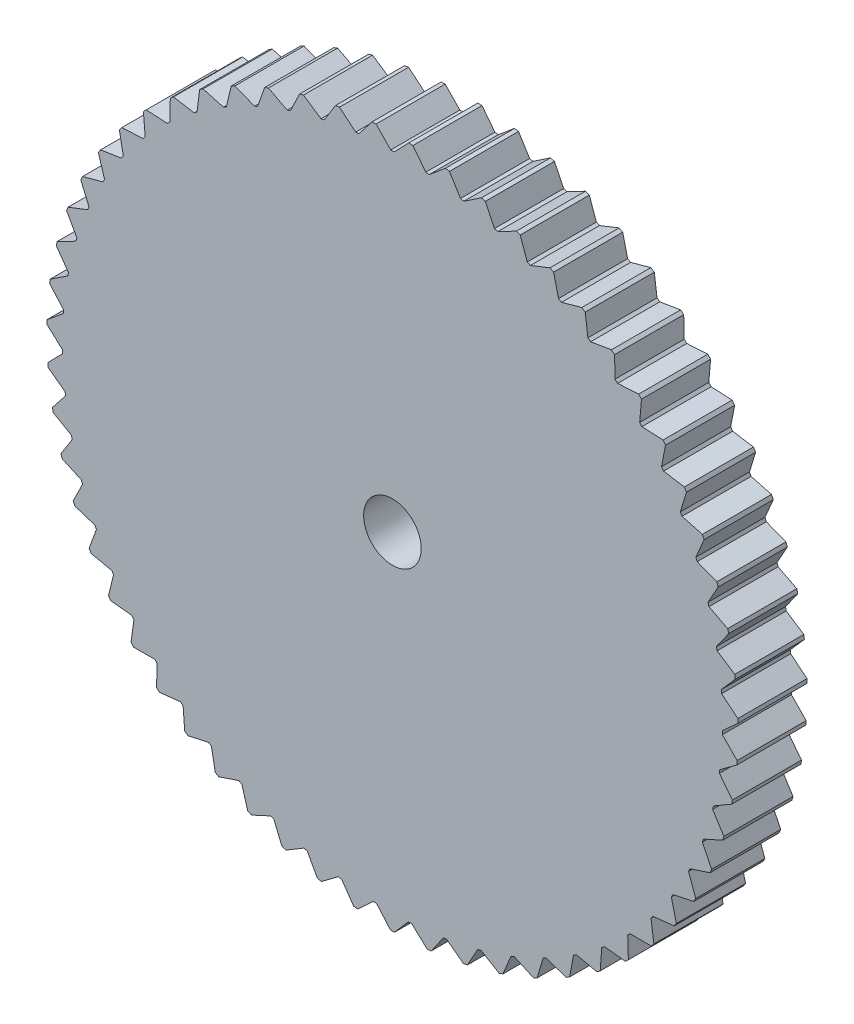
SolidWorks part; units mm, degrees
ref_plane "Front Plane" through (0, 0, 0) normal (0, 0, 1) x (1, 0, 0)
ref_plane "Top Plane" through (0, 0, 0) normal (0, 1, 0) x (1, 0, 0)
ref_plane "Right Plane" through (0, 0, 0) normal (1, 0, 0) x (0, 0, -1)
sketch "Sketch1" plane through (0, 0, 0) normal (0, 0, 1) x (1, 0, 0)
  line L0 (0, 0) -> (0, 60) construction
  line L1 (-3, 61) -> (-0.3, 57.3) construction
  line L2 (0.3, 57.3) -> (3, 61) construction
  line L3 (-0.3, 57.3) -> (0.3, 57.3) construction
  line L4 (-3, 61) -> (3, 61) construction
  line L5 (7.7766, 56.7706) -> (10.9364, 60.0866) construction
  line L6 (4.9878, 60.8697) -> (7.1817, 56.8489) construction
  line L7 (4.9878, 60.8697) -> (10.9364, 60.0866) construction
  line L8 (7.1817, 56.8489) -> (7.7766, 56.7706) construction
  line L9 (15.1201, 55.2699) -> (18.6857, 58.145) construction
  line L10 (12.8902, 59.6979) -> (14.5406, 55.4252) construction
  line L11 (12.8902, 59.6979) -> (18.6857, 58.145) construction
  line L12 (14.5406, 55.4252) -> (15.1201, 55.2699) construction
  line L13 (22.2049, 52.8235) -> (26.1153, 55.2086) construction
  line L14 (20.5721, 57.5047) -> (21.6506, 53.0531) construction
  line L15 (20.5721, 57.5047) -> (26.1153, 55.2086) construction
  line L16 (21.6506, 53.0531) -> (22.2049, 52.8235) construction
  line L17 (28.9098, 49.4733) -> (33.0981, 51.3275) construction
  line L18 (27.9019, 54.3275) -> (28.3902, 49.7733) construction
  line L19 (27.9019, 54.3275) -> (33.0981, 51.3275) construction
  line L20 (28.3902, 49.7733) -> (28.9098, 49.4733) construction
  line L21 (35.12, 45.2765) -> (39.5145, 46.5683) construction
  line L22 (34.7544, 50.2208) -> (34.644, 45.6418) construction
  line L23 (34.7544, 50.2208) -> (39.5145, 46.5683) construction
  line L24 (34.644, 45.6418) -> (35.12, 45.2765) construction
  line L25 (40.7294, 40.3051) -> (45.2548, 41.0122) construction
  line L26 (41.0122, 45.2548) -> (40.3051, 40.7294) construction
  line L27 (41.0122, 45.2548) -> (45.2548, 41.0122) construction
  line L28 (40.3051, 40.7294) -> (40.7294, 40.3051) construction
  line L29 (45.6418, 34.644) -> (50.2208, 34.7544) construction
  line L30 (46.5683, 39.5145) -> (45.2765, 35.12) construction
  line L31 (46.5683, 39.5145) -> (50.2208, 34.7544) construction
  line L32 (45.2765, 35.12) -> (45.6418, 34.644) construction
  line L33 (49.7733, 28.3902) -> (54.3275, 27.9019) construction
  line L34 (51.3275, 33.0981) -> (49.4733, 28.9098) construction
  line L35 (51.3275, 33.0981) -> (54.3275, 27.9019) construction
  line L36 (49.4733, 28.9098) -> (49.7733, 28.3902) construction
  line L37 (53.0531, 21.6506) -> (57.5047, 20.5721) construction
  line L38 (55.2086, 26.1153) -> (52.8235, 22.2049) construction
  line L39 (55.2086, 26.1153) -> (57.5047, 20.5721) construction
  line L40 (52.8235, 22.2049) -> (53.0531, 21.6506) construction
  line L41 (55.4252, 14.5406) -> (59.6979, 12.8902) construction
  line L42 (58.145, 18.6857) -> (55.2699, 15.1201) construction
  line L43 (58.145, 18.6857) -> (59.6979, 12.8902) construction
  line L44 (55.2699, 15.1201) -> (55.4252, 14.5406) construction
  line L45 (56.8489, 7.1817) -> (60.8697, 4.9878) construction
  line L46 (60.0866, 10.9364) -> (56.7706, 7.7766) construction
  line L47 (60.0866, 10.9364) -> (60.8697, 4.9878) construction
  line L48 (56.7706, 7.7766) -> (56.8489, 7.1817) construction
  line L49 (57.3, -0.3) -> (61, -3) construction
  line L50 (61, 3) -> (57.3, 0.3) construction
  line L51 (61, 3) -> (61, -3) construction
  line L52 (57.3, 0.3) -> (57.3, -0.3) construction
  line L53 (56.7706, -7.7766) -> (60.0866, -10.9364) construction
  line L54 (60.8697, -4.9878) -> (56.8489, -7.1817) construction
  line L55 (60.8697, -4.9878) -> (60.0866, -10.9364) construction
  line L56 (56.8489, -7.1817) -> (56.7706, -7.7766) construction
  line L57 (55.2699, -15.1201) -> (58.145, -18.6857) construction
  line L58 (59.6979, -12.8902) -> (55.4252, -14.5406) construction
  line L59 (59.6979, -12.8902) -> (58.145, -18.6857) construction
  line L60 (55.4252, -14.5406) -> (55.2699, -15.1201) construction
  line L61 (52.8235, -22.2049) -> (55.2086, -26.1153) construction
  line L62 (57.5047, -20.5721) -> (53.0531, -21.6506) construction
  line L63 (57.5047, -20.5721) -> (55.2086, -26.1153) construction
  line L64 (53.0531, -21.6506) -> (52.8235, -22.2049) construction
  line L65 (49.4733, -28.9098) -> (51.3275, -33.0981) construction
  line L66 (54.3275, -27.9019) -> (49.7733, -28.3902) construction
  line L67 (54.3275, -27.9019) -> (51.3275, -33.0981) construction
  line L68 (49.7733, -28.3902) -> (49.4733, -28.9098) construction
  line L69 (45.2765, -35.12) -> (46.5683, -39.5145) construction
  line L70 (50.2208, -34.7544) -> (45.6418, -34.644) construction
  line L71 (50.2208, -34.7544) -> (46.5683, -39.5145) construction
  line L72 (45.6418, -34.644) -> (45.2765, -35.12) construction
  line L73 (40.3051, -40.7294) -> (41.0122, -45.2548) construction
  line L74 (45.2548, -41.0122) -> (40.7294, -40.3051) construction
  line L75 (45.2548, -41.0122) -> (41.0122, -45.2548) construction
  line L76 (40.7294, -40.3051) -> (40.3051, -40.7294) construction
  line L77 (34.644, -45.6418) -> (34.7544, -50.2208) construction
  line L78 (39.5145, -46.5683) -> (35.12, -45.2765) construction
  line L79 (39.5145, -46.5683) -> (34.7544, -50.2208) construction
  line L80 (35.12, -45.2765) -> (34.644, -45.6418) construction
  line L81 (28.3902, -49.7733) -> (27.9019, -54.3275) construction
  line L82 (33.0981, -51.3275) -> (28.9098, -49.4733) construction
  line L83 (33.0981, -51.3275) -> (27.9019, -54.3275) construction
  line L84 (28.9098, -49.4733) -> (28.3902, -49.7733) construction
  line L85 (21.6506, -53.0531) -> (20.5721, -57.5047) construction
  line L86 (26.1153, -55.2086) -> (22.2049, -52.8235) construction
  line L87 (26.1153, -55.2086) -> (20.5721, -57.5047) construction
  line L88 (22.2049, -52.8235) -> (21.6506, -53.0531) construction
  line L89 (14.5406, -55.4252) -> (12.8902, -59.6979) construction
  line L90 (18.6857, -58.145) -> (15.1201, -55.2699) construction
  line L91 (18.6857, -58.145) -> (12.8902, -59.6979) construction
  line L92 (15.1201, -55.2699) -> (14.5406, -55.4252) construction
  line L93 (7.1817, -56.8489) -> (4.9878, -60.8697) construction
  line L94 (10.9364, -60.0866) -> (7.7766, -56.7706) construction
  line L95 (10.9364, -60.0866) -> (4.9878, -60.8697) construction
  line L96 (7.7766, -56.7706) -> (7.1817, -56.8489) construction
  line L97 (-0.3, -57.3) -> (-3, -61) construction
  line L98 (3, -61) -> (0.3, -57.3) construction
  line L99 (3, -61) -> (-3, -61) construction
  line L100 (0.3, -57.3) -> (-0.3, -57.3) construction
  line L101 (-7.7766, -56.7706) -> (-10.9364, -60.0866) construction
  line L102 (-4.9878, -60.8697) -> (-7.1817, -56.8489) construction
  line L103 (-4.9878, -60.8697) -> (-10.9364, -60.0866) construction
  line L104 (-7.1817, -56.8489) -> (-7.7766, -56.7706) construction
  line L105 (-15.1201, -55.2699) -> (-18.6857, -58.145) construction
  line L106 (-12.8902, -59.6979) -> (-14.5406, -55.4252) construction
  line L107 (-12.8902, -59.6979) -> (-18.6857, -58.145) construction
  line L108 (-14.5406, -55.4252) -> (-15.1201, -55.2699) construction
  line L109 (-22.2049, -52.8235) -> (-26.1153, -55.2086) construction
  line L110 (-20.5721, -57.5047) -> (-21.6506, -53.0531) construction
  line L111 (-20.5721, -57.5047) -> (-26.1153, -55.2086) construction
  line L112 (-21.6506, -53.0531) -> (-22.2049, -52.8235) construction
  line L113 (-28.9098, -49.4733) -> (-33.0981, -51.3275) construction
  line L114 (-27.9019, -54.3275) -> (-28.3902, -49.7733) construction
  line L115 (-27.9019, -54.3275) -> (-33.0981, -51.3275) construction
  line L116 (-28.3902, -49.7733) -> (-28.9098, -49.4733) construction
  line L117 (-35.12, -45.2765) -> (-39.5145, -46.5683) construction
  line L118 (-34.7544, -50.2208) -> (-34.644, -45.6418) construction
  line L119 (-34.7544, -50.2208) -> (-39.5145, -46.5683) construction
  line L120 (-34.644, -45.6418) -> (-35.12, -45.2765) construction
  line L121 (-40.7294, -40.3051) -> (-45.2548, -41.0122) construction
  line L122 (-41.0122, -45.2548) -> (-40.3051, -40.7294) construction
  line L123 (-41.0122, -45.2548) -> (-45.2548, -41.0122) construction
  line L124 (-40.3051, -40.7294) -> (-40.7294, -40.3051) construction
  line L125 (-45.6418, -34.644) -> (-50.2208, -34.7544) construction
  line L126 (-46.5683, -39.5145) -> (-45.2765, -35.12) construction
  line L127 (-46.5683, -39.5145) -> (-50.2208, -34.7544) construction
  line L128 (-45.2765, -35.12) -> (-45.6418, -34.644) construction
  line L129 (-49.7733, -28.3902) -> (-54.3275, -27.9019) construction
  line L130 (-51.3275, -33.0981) -> (-49.4733, -28.9098) construction
  line L131 (-51.3275, -33.0981) -> (-54.3275, -27.9019) construction
  line L132 (-49.4733, -28.9098) -> (-49.7733, -28.3902) construction
  line L133 (-53.0531, -21.6506) -> (-57.5047, -20.5721) construction
  line L134 (-55.2086, -26.1153) -> (-52.8235, -22.2049) construction
  line L135 (-55.2086, -26.1153) -> (-57.5047, -20.5721) construction
  line L136 (-52.8235, -22.2049) -> (-53.0531, -21.6506) construction
  line L137 (-55.4252, -14.5406) -> (-59.6979, -12.8902) construction
  line L138 (-58.145, -18.6857) -> (-55.2699, -15.1201) construction
  line L139 (-58.145, -18.6857) -> (-59.6979, -12.8902) construction
  line L140 (-55.2699, -15.1201) -> (-55.4252, -14.5406) construction
  line L141 (-56.8489, -7.1817) -> (-60.8697, -4.9878) construction
  line L142 (-60.0866, -10.9364) -> (-56.7706, -7.7766) construction
  line L143 (-60.0866, -10.9364) -> (-60.8697, -4.9878) construction
  line L144 (-56.7706, -7.7766) -> (-56.8489, -7.1817) construction
  line L145 (-57.3, 0.3) -> (-61, 3) construction
  line L146 (-61, -3) -> (-57.3, -0.3) construction
  line L147 (-61, -3) -> (-61, 3) construction
  line L148 (-57.3, -0.3) -> (-57.3, 0.3) construction
  line L149 (-56.7706, 7.7766) -> (-60.0866, 10.9364) construction
  line L150 (-60.8697, 4.9878) -> (-56.8489, 7.1817) construction
  line L151 (-60.8697, 4.9878) -> (-60.0866, 10.9364) construction
  line L152 (-56.8489, 7.1817) -> (-56.7706, 7.7766) construction
  line L153 (-55.2699, 15.1201) -> (-58.145, 18.6857) construction
  line L154 (-59.6979, 12.8902) -> (-55.4252, 14.5406) construction
  line L155 (-59.6979, 12.8902) -> (-58.145, 18.6857) construction
  line L156 (-55.4252, 14.5406) -> (-55.2699, 15.1201) construction
  line L157 (-52.8235, 22.2049) -> (-55.2086, 26.1153) construction
  line L158 (-57.5047, 20.5721) -> (-53.0531, 21.6506) construction
  line L159 (-57.5047, 20.5721) -> (-55.2086, 26.1153) construction
  line L160 (-53.0531, 21.6506) -> (-52.8235, 22.2049) construction
  line L161 (-49.4733, 28.9098) -> (-51.3275, 33.0981) construction
  line L162 (-54.3275, 27.9019) -> (-49.7733, 28.3902) construction
  line L163 (-54.3275, 27.9019) -> (-51.3275, 33.0981) construction
  line L164 (-49.7733, 28.3902) -> (-49.4733, 28.9098) construction
  line L165 (-45.2765, 35.12) -> (-46.5683, 39.5145) construction
  line L166 (-50.2208, 34.7544) -> (-45.6418, 34.644) construction
  line L167 (-50.2208, 34.7544) -> (-46.5683, 39.5145) construction
  line L168 (-45.6418, 34.644) -> (-45.2765, 35.12) construction
  line L169 (-40.3051, 40.7294) -> (-41.0122, 45.2548) construction
  line L170 (-45.2548, 41.0122) -> (-40.7294, 40.3051) construction
  line L171 (-45.2548, 41.0122) -> (-41.0122, 45.2548) construction
  line L172 (-40.7294, 40.3051) -> (-40.3051, 40.7294) construction
  line L173 (-34.644, 45.6418) -> (-34.7544, 50.2208) construction
  line L174 (-39.5145, 46.5683) -> (-35.12, 45.2765) construction
  line L175 (-39.5145, 46.5683) -> (-34.7544, 50.2208) construction
  line L176 (-35.12, 45.2765) -> (-34.644, 45.6418) construction
  line L177 (-28.3902, 49.7733) -> (-27.9019, 54.3275) construction
  line L178 (-33.0981, 51.3275) -> (-28.9098, 49.4733) construction
  line L179 (-33.0981, 51.3275) -> (-27.9019, 54.3275) construction
  line L180 (-28.9098, 49.4733) -> (-28.3902, 49.7733) construction
  line L181 (-21.6506, 53.0531) -> (-20.5721, 57.5047) construction
  line L182 (-26.1153, 55.2086) -> (-22.2049, 52.8235) construction
  line L183 (-26.1153, 55.2086) -> (-20.5721, 57.5047) construction
  line L184 (-22.2049, 52.8235) -> (-21.6506, 53.0531) construction
  line L185 (-14.5406, 55.4252) -> (-12.8902, 59.6979) construction
  line L186 (-18.6857, 58.145) -> (-15.1201, 55.2699) construction
  line L187 (-18.6857, 58.145) -> (-12.8902, 59.6979) construction
  line L188 (-15.1201, 55.2699) -> (-14.5406, 55.4252) construction
  line L189 (-7.1817, 56.8489) -> (-4.9878, 60.8697) construction
  line L190 (-10.9364, 60.0866) -> (-7.7766, 56.7706) construction
  line L191 (-10.9364, 60.0866) -> (-4.9878, 60.8697) construction
  line L192 (-7.7766, 56.7706) -> (-7.1817, 56.8489) construction
  circle A0 centre (0, 0) radius 60
  circle A1 centre (0, 0) radius 5
  point P200 (0, 0)
  dimension "D1" = 10
  dimension "D2" = 120
  dimension "D3" = 0.6
  dimension "D4" = 6
  dimension "D5" = 3.7
  dimension "D6" = 1
  dimension "D7" = 48
extrude "Boss-Extrude1" add sketch "Sketch1" along normal blind 12 contours A1 | A0
sketch "Sketch2" plane through (0, 0, 12) normal (0, 0, 1) x (1, 0, 0)
  line L0 (0, 0) -> (0, 60) construction
  line L1 (-3, 60.1) -> (-0.3, 57.3)
  line L2 (0.3, 57.3) -> (3, 60.1)
  line L3 (-0.3, 57.3) -> (0.3, 57.3)
  line L4 (-3, 60.1) -> (3, 60.1)
  line L5 (3.4052, 60.0784) -> (5.7923, 57.0073)
  line L6 (6.3889, 56.9435) -> (9.3712, 59.4406)
  line L7 (5.7923, 57.0073) -> (6.3889, 56.9435)
  line L8 (3.4052, 60.0784) -> (9.3712, 59.4406)
  line L9 (0, 0) -> (6.3776, 59.6601) construction
  line L10 (9.7719, 59.3761) -> (11.819, 56.0686)
  line L11 (12.4054, 55.9418) -> (15.6363, 58.1078)
  line L12 (11.819, 56.0686) -> (12.4054, 55.9418)
  line L13 (9.7719, 59.3761) -> (15.6363, 58.1078)
  line L14 (0, 0) -> (12.683, 58.6442) construction
  line L15 (16.0278, 58.001) -> (17.7118, 54.4947)
  line L16 (18.2814, 54.3063) -> (21.7242, 56.1166)
  line L17 (17.7118, 54.4947) -> (18.2814, 54.3063)
  line L18 (16.0278, 58.001) -> (21.7242, 56.1166)
  line L19 (0, 0) -> (18.8446, 56.9639) construction
  line L20 (22.1021, 55.9688) -> (23.4039, 52.3033)
  line L21 (23.9502, 52.0554) -> (27.566, 53.4895)
  line L22 (23.4039, 52.3033) -> (23.9502, 52.0554)
  line L23 (22.1021, 55.9688) -> (27.566, 53.4895)
  line L24 (0, 0) -> (24.7927, 54.6381) construction
  line L25 (27.9261, 53.3024) -> (28.8308, 49.5193)
  line L26 (29.3477, 49.2147) -> (33.0954, 50.2564)
  line L27 (28.8308, 49.5193) -> (29.3477, 49.2147)
  line L28 (27.9261, 53.3024) -> (33.0954, 50.2564)
  line L29 (0, 0) -> (30.4599, 51.6932) construction
  line L30 (33.4335, 50.0321) -> (33.931, 46.1743)
  line L31 (34.4127, 45.8165) -> (38.2498, 46.4539)
  line L32 (33.931, 46.1743) -> (34.4127, 45.8165)
  line L33 (33.4335, 50.0321) -> (38.2498, 46.4539)
  line L34 (0, 0) -> (35.782, 48.1627) construction
  line L35 (38.5622, 46.1949) -> (38.6468, 42.3061)
  line L36 (39.0877, 41.8991) -> (42.9709, 42.125)
  line L37 (38.6468, 42.3061) -> (39.0877, 41.8991)
  line L38 (38.5622, 46.1949) -> (42.9709, 42.125)
  line L39 (0, 0) -> (40.6987, 44.0864) construction
  line L40 (43.254, 41.8342) -> (42.9248, 37.9585)
  line L41 (43.3199, 37.5069) -> (47.205, 37.3188)
  line L42 (42.9248, 37.9585) -> (43.3199, 37.5069)
  line L43 (43.254, 41.8342) -> (47.205, 37.3188)
  line L44 (0, 0) -> (45.1542, 39.5107) construction
  line L45 (47.4556, 36.9996) -> (46.7163, 33.1808)
  line L46 (47.0612, 32.6898) -> (50.9044, 32.0898)
  line L47 (46.7163, 33.1808) -> (47.0612, 32.6898)
  line L48 (47.4556, 36.9996) -> (50.9044, 32.0898)
  line L49 (0, 0) -> (49.0982, 34.4872) construction
  line L50 (51.1196, 31.7458) -> (49.9786, 28.0272)
  line L51 (50.2693, 27.5023) -> (54.0269, 26.4972)
  line L52 (49.9786, 28.0272) -> (50.2693, 27.5023)
  line L53 (51.1196, 31.7458) -> (54.0269, 26.4972)
  line L54 (0, 0) -> (52.4858, 29.0731) construction
  line L55 (54.2044, 26.1323) -> (52.6745, 22.556)
  line L56 (52.9078, 22.0032) -> (56.5373, 20.6044)
  line L57 (52.6745, 22.556) -> (52.9078, 22.0032)
  line L58 (54.2044, 26.1323) -> (56.5373, 20.6044)
  line L59 (0, 0) -> (55.2787, 23.3295) construction
  line L60 (56.675, 20.2227) -> (54.7737, 16.8293)
  line L61 (54.9469, 16.2548) -> (58.4071, 14.4781)
  line L62 (54.7737, 16.8293) -> (54.9469, 16.2548)
  line L63 (56.675, 20.2227) -> (58.4071, 14.4781)
  line L64 (0, 0) -> (57.4453, 17.3215) construction
  line L65 (58.5034, 14.0839) -> (56.2522, 10.9118)
  line L66 (56.3634, 10.3222) -> (59.6152, 8.1878)
  line L67 (56.2522, 10.9118) -> (56.3634, 10.3222)
  line L68 (58.5034, 14.0839) -> (59.6152, 8.1878)
  line L69 (0, 0) -> (58.961, 11.1173) construction
  line L70 (59.669, 7.7856) -> (57.0934, 4.8708)
  line L71 (57.1413, 4.2727) -> (60.1478, 1.8047)
  line L72 (57.0934, 4.8708) -> (57.1413, 4.2727)
  line L73 (59.669, 7.7856) -> (60.1478, 1.8047)
  line L74 (0, 0) -> (59.8087, 4.7872) construction
  line L75 (60.1586, 1.399) -> (57.2877, -1.2255)
  line L76 (57.2717, -1.8252) -> (59.9988, -4.5988)
  line L77 (57.2877, -1.2255) -> (57.2717, -1.8252)
  line L78 (60.1586, 1.399) -> (59.9988, -4.5988)
  line L79 (0, 0) -> (59.9787, -1.5972) construction
  line L80 (59.9665, -5.0033) -> (56.8329, -7.3078)
  line L81 (56.7532, -7.9025) -> (59.1701, -10.9503)
  line L82 (56.8329, -7.3078) -> (56.7532, -7.9025)
  line L83 (59.9665, -5.0033) -> (59.1701, -10.9503)
  line L84 (0, 0) -> (59.4692, -7.9635) construction
  line L85 (59.0949, -11.349) -> (55.7341, -13.3074)
  line L86 (55.5917, -13.8902) -> (57.671, -17.1776)
  line L87 (55.7341, -13.3074) -> (55.5917, -13.8902)
  line L88 (59.0949, -11.349) -> (57.671, -17.1776)
  line L89 (0, 0) -> (58.2858, -14.2396) construction
  line L90 (57.5538, -17.5662) -> (54.0039, -19.1562)
  line L91 (53.8004, -19.7206) -> (55.5184, -23.2104)
  line L92 (54.0039, -19.1562) -> (53.8004, -19.7206)
  line L93 (57.5538, -17.5662) -> (55.5184, -23.2104)
  line L94 (0, 0) -> (56.442, -20.3543) construction
  line L95 (55.3606, -23.5842) -> (51.6618, -24.7879)
  line L96 (51.3994, -25.3275) -> (52.7367, -28.9801)
  line L97 (51.6618, -24.7879) -> (51.3994, -25.3275)
  line L98 (55.3606, -23.5842) -> (52.7367, -28.9801)
  line L99 (0, 0) -> (53.9587, -26.2384) construction
  line L100 (52.5401, -29.3351) -> (48.7343, -30.1388)
  line L101 (48.4161, -30.6474) -> (49.3576, -34.4215)
  line L102 (48.7343, -30.1388) -> (48.4161, -30.6474)
  line L103 (52.5401, -29.3351) -> (49.3576, -34.4215)
  line L104 (0, 0) -> (50.8641, -31.8253) construction
  line L105 (49.1243, -34.7536) -> (45.2547, -35.1482)
  line L106 (44.8841, -35.6201) -> (45.4192, -39.4729)
  line L107 (45.2547, -35.1482) -> (44.8841, -35.6201)
  line L108 (49.1243, -34.7536) -> (45.4192, -39.4729)
  line L109 (0, 0) -> (47.1931, -37.0515) construction
  line L110 (45.1519, -39.7783) -> (41.2623, -39.7593)
  line L111 (40.8437, -40.1892) -> (40.9662, -44.077)
  line L112 (41.2623, -39.7593) -> (40.8437, -40.1892)
  line L113 (45.1519, -39.7783) -> (40.9662, -44.077)
  line L114 (0, 0) -> (42.9874, -41.8579) construction
  line L115 (40.668, -44.3523) -> (36.8023, -43.92)
  line L116 (36.3404, -44.303) -> (36.049, -48.1818)
  line L117 (36.8023, -43.92) -> (36.3404, -44.303)
  line L118 (40.668, -44.3523) -> (36.049, -48.1818)
  line L119 (0, 0) -> (38.2947, -46.19) construction
  line L120 (35.7232, -48.4238) -> (31.9254, -47.583)
  line L121 (31.4254, -47.9147) -> (30.7233, -51.7406)
  line L122 (31.9254, -47.583) -> (31.4254, -47.9147)
  line L123 (35.7232, -48.4238) -> (30.7233, -51.7406)
  line L124 (0, 0) -> (33.168, -49.9988) construction
  line L125 (30.3737, -51.9466) -> (26.6868, -50.7069)
  line L126 (26.1544, -50.9836) -> (25.0496, -54.7131)
  line L127 (26.6868, -50.7069) -> (26.1544, -50.9836)
  line L128 (30.3737, -51.9466) -> (25.0496, -54.7131)
  line L129 (0, 0) -> (27.6656, -53.2411) construction
  line L130 (24.6801, -54.8808) -> (21.1458, -53.2563)
  line L131 (20.587, -53.4748) -> (19.092, -57.0658)
  line L132 (21.1458, -53.2563) -> (20.587, -53.4748)
  line L133 (24.6801, -54.8808) -> (19.092, -57.0658)
  line L134 (0, 0) -> (21.8496, -55.8802) construction
  line L135 (18.7068, -57.1932) -> (15.3652, -55.2023)
  line L136 (14.7863, -55.3601) -> (12.9182, -58.7719)
  line L137 (15.3652, -55.2023) -> (14.7863, -55.3601)
  line L138 (18.7068, -57.1932) -> (12.9182, -58.7719)
  line L139 (0, 0) -> (15.7862, -57.8861) construction
  line L140 (12.5215, -58.8576) -> (9.4105, -56.5228)
  line L141 (8.8182, -56.6182) -> (6.5979, -59.812)
  line L142 (9.4105, -56.5228) -> (8.8182, -56.6182)
  line L143 (12.5215, -58.8576) -> (6.5979, -59.812)
  line L144 (0, 0) -> (9.5438, -59.2361) construction
  line L145 (6.1944, -59.8552) -> (3.3492, -57.2028)
  line L146 (2.7501, -57.2348) -> (0.2029, -60.1745)
  line L147 (3.3492, -57.2028) -> (2.7501, -57.2348)
  line L148 (6.1944, -59.8552) -> (0.2029, -60.1745)
  line L149 (0, 0) -> (3.1933, -59.915) construction
  line L150 (-0.2029, -60.1745) -> (-2.7501, -57.2348)
  line L151 (-3.3492, -57.2028) -> (-6.1944, -59.8552)
  line L152 (-2.7501, -57.2348) -> (-3.3492, -57.2028)
  line L153 (-0.2029, -60.1745) -> (-6.1944, -59.8552)
  line L154 (0, 0) -> (-3.1933, -59.915) construction
  line L155 (-6.5979, -59.812) -> (-8.8182, -56.6182)
  line L156 (-9.4105, -56.5228) -> (-12.5215, -58.8576)
  line L157 (-8.8182, -56.6182) -> (-9.4105, -56.5228)
  line L158 (-6.5979, -59.812) -> (-12.5215, -58.8576)
  line L159 (0, 0) -> (-9.5438, -59.2361) construction
  line L160 (-12.9182, -58.7719) -> (-14.7863, -55.3601)
  line L161 (-15.3652, -55.2023) -> (-18.7068, -57.1932)
  line L162 (-14.7863, -55.3601) -> (-15.3652, -55.2023)
  line L163 (-12.9182, -58.7719) -> (-18.7068, -57.1932)
  line L164 (0, 0) -> (-15.7862, -57.8861) construction
  line L165 (-19.092, -57.0658) -> (-20.587, -53.4748)
  line L166 (-21.1458, -53.2563) -> (-24.6801, -54.8808)
  line L167 (-20.587, -53.4748) -> (-21.1458, -53.2563)
  line L168 (-19.092, -57.0658) -> (-24.6801, -54.8808)
  line L169 (0, 0) -> (-21.8496, -55.8802) construction
  line L170 (-25.0496, -54.7131) -> (-26.1544, -50.9836)
  line L171 (-26.6868, -50.7069) -> (-30.3737, -51.9466)
  line L172 (-26.1544, -50.9836) -> (-26.6868, -50.7069)
  line L173 (-25.0496, -54.7131) -> (-30.3737, -51.9466)
  line L174 (0, 0) -> (-27.6656, -53.2411) construction
  line L175 (-30.7233, -51.7406) -> (-31.4254, -47.9147)
  line L176 (-31.9254, -47.583) -> (-35.7232, -48.4238)
  line L177 (-31.4254, -47.9147) -> (-31.9254, -47.583)
  line L178 (-30.7233, -51.7406) -> (-35.7232, -48.4238)
  line L179 (0, 0) -> (-33.168, -49.9988) construction
  line L180 (-36.049, -48.1818) -> (-36.3404, -44.303)
  line L181 (-36.8023, -43.92) -> (-40.668, -44.3523)
  line L182 (-36.3404, -44.303) -> (-36.8023, -43.92)
  line L183 (-36.049, -48.1818) -> (-40.668, -44.3523)
  line L184 (0, 0) -> (-38.2947, -46.19) construction
  line L185 (-40.9662, -44.077) -> (-40.8437, -40.1892)
  line L186 (-41.2623, -39.7593) -> (-45.1519, -39.7783)
  line L187 (-40.8437, -40.1892) -> (-41.2623, -39.7593)
  line L188 (-40.9662, -44.077) -> (-45.1519, -39.7783)
  line L189 (0, 0) -> (-42.9874, -41.8579) construction
  line L190 (-45.4192, -39.4729) -> (-44.8841, -35.6201)
  line L191 (-45.2547, -35.1482) -> (-49.1243, -34.7536)
  line L192 (-44.8841, -35.6201) -> (-45.2547, -35.1482)
  line L193 (-45.4192, -39.4729) -> (-49.1243, -34.7536)
  line L194 (0, 0) -> (-47.1931, -37.0515) construction
  line L195 (-49.3576, -34.4215) -> (-48.4161, -30.6474)
  line L196 (-48.7343, -30.1388) -> (-52.5401, -29.3351)
  line L197 (-48.4161, -30.6474) -> (-48.7343, -30.1388)
  line L198 (-49.3576, -34.4215) -> (-52.5401, -29.3351)
  line L199 (0, 0) -> (-50.8641, -31.8253) construction
  line L200 (-52.7367, -28.9801) -> (-51.3994, -25.3275)
  line L201 (-51.6618, -24.7879) -> (-55.3606, -23.5842)
  line L202 (-51.3994, -25.3275) -> (-51.6618, -24.7879)
  line L203 (-52.7367, -28.9801) -> (-55.3606, -23.5842)
  line L204 (0, 0) -> (-53.9587, -26.2384) construction
  line L205 (-55.5184, -23.2104) -> (-53.8004, -19.7206)
  line L206 (-54.0039, -19.1562) -> (-57.5538, -17.5662)
  line L207 (-53.8004, -19.7206) -> (-54.0039, -19.1562)
  line L208 (-55.5184, -23.2104) -> (-57.5538, -17.5662)
  line L209 (0, 0) -> (-56.442, -20.3543) construction
  line L210 (-57.671, -17.1776) -> (-55.5917, -13.8902)
  line L211 (-55.7341, -13.3074) -> (-59.0949, -11.349)
  line L212 (-55.5917, -13.8902) -> (-55.7341, -13.3074)
  line L213 (-57.671, -17.1776) -> (-59.0949, -11.349)
  line L214 (0, 0) -> (-58.2858, -14.2396) construction
  line L215 (-59.1701, -10.9503) -> (-56.7532, -7.9025)
  line L216 (-56.8329, -7.3078) -> (-59.9665, -5.0033)
  line L217 (-56.7532, -7.9025) -> (-56.8329, -7.3078)
  line L218 (-59.1701, -10.9503) -> (-59.9665, -5.0033)
  line L219 (0, 0) -> (-59.4692, -7.9635) construction
  line L220 (-59.9988, -4.5988) -> (-57.2717, -1.8252)
  line L221 (-57.2877, -1.2255) -> (-60.1586, 1.399)
  line L222 (-57.2717, -1.8252) -> (-57.2877, -1.2255)
  line L223 (-59.9988, -4.5988) -> (-60.1586, 1.399)
  line L224 (0, 0) -> (-59.9787, -1.5972) construction
  line L225 (-60.1478, 1.8047) -> (-57.1413, 4.2727)
  line L226 (-57.0934, 4.8708) -> (-59.669, 7.7856)
  line L227 (-57.1413, 4.2727) -> (-57.0934, 4.8708)
  line L228 (-60.1478, 1.8047) -> (-59.669, 7.7856)
  line L229 (0, 0) -> (-59.8087, 4.7872) construction
  line L230 (-59.6152, 8.1878) -> (-56.3634, 10.3222)
  line L231 (-56.2522, 10.9118) -> (-58.5034, 14.0839)
  line L232 (-56.3634, 10.3222) -> (-56.2522, 10.9118)
  line L233 (-59.6152, 8.1878) -> (-58.5034, 14.0839)
  line L234 (0, 0) -> (-58.961, 11.1173) construction
  line L235 (-58.4071, 14.4781) -> (-54.9469, 16.2548)
  line L236 (-54.7737, 16.8293) -> (-56.675, 20.2227)
  line L237 (-54.9469, 16.2548) -> (-54.7737, 16.8293)
  line L238 (-58.4071, 14.4781) -> (-56.675, 20.2227)
  line L239 (0, 0) -> (-57.4453, 17.3215) construction
  line L240 (-56.5373, 20.6044) -> (-52.9078, 22.0032)
  line L241 (-52.6745, 22.556) -> (-54.2044, 26.1323)
  line L242 (-52.9078, 22.0032) -> (-52.6745, 22.556)
  line L243 (-56.5373, 20.6044) -> (-54.2044, 26.1323)
  line L244 (0, 0) -> (-55.2787, 23.3295) construction
  line L245 (-54.0269, 26.4972) -> (-50.2693, 27.5023)
  line L246 (-49.9786, 28.0272) -> (-51.1196, 31.7458)
  line L247 (-50.2693, 27.5023) -> (-49.9786, 28.0272)
  line L248 (-54.0269, 26.4972) -> (-51.1196, 31.7458)
  line L249 (0, 0) -> (-52.4858, 29.0731) construction
  line L250 (-50.9044, 32.0898) -> (-47.0612, 32.6898)
  line L251 (-46.7163, 33.1808) -> (-47.4556, 36.9996)
  line L252 (-47.0612, 32.6898) -> (-46.7163, 33.1808)
  line L253 (-50.9044, 32.0898) -> (-47.4556, 36.9996)
  line L254 (0, 0) -> (-49.0982, 34.4872) construction
  line L255 (-47.205, 37.3188) -> (-43.3199, 37.5069)
  line L256 (-42.9248, 37.9585) -> (-43.254, 41.8342)
  line L257 (-43.3199, 37.5069) -> (-42.9248, 37.9585)
  line L258 (-47.205, 37.3188) -> (-43.254, 41.8342)
  line L259 (0, 0) -> (-45.1542, 39.5107) construction
  line L260 (-42.9709, 42.125) -> (-39.0877, 41.8991)
  line L261 (-38.6468, 42.3061) -> (-38.5622, 46.1949)
  line L262 (-39.0877, 41.8991) -> (-38.6468, 42.3061)
  line L263 (-42.9709, 42.125) -> (-38.5622, 46.1949)
  line L264 (0, 0) -> (-40.6987, 44.0864) construction
  line L265 (-38.2498, 46.4539) -> (-34.4127, 45.8165)
  line L266 (-33.931, 46.1743) -> (-33.4335, 50.0321)
  line L267 (-34.4127, 45.8165) -> (-33.931, 46.1743)
  line L268 (-38.2498, 46.4539) -> (-33.4335, 50.0321)
  line L269 (0, 0) -> (-35.782, 48.1627) construction
  line L270 (-33.0954, 50.2564) -> (-29.3477, 49.2147)
  line L271 (-28.8308, 49.5193) -> (-27.9261, 53.3024)
  line L272 (-29.3477, 49.2147) -> (-28.8308, 49.5193)
  line L273 (-33.0954, 50.2564) -> (-27.9261, 53.3024)
  line L274 (0, 0) -> (-30.4599, 51.6932) construction
  line L275 (-27.566, 53.4895) -> (-23.9502, 52.0554)
  line L276 (-23.4039, 52.3033) -> (-22.1021, 55.9688)
  line L277 (-23.9502, 52.0554) -> (-23.4039, 52.3033)
  line L278 (-27.566, 53.4895) -> (-22.1021, 55.9688)
  line L279 (0, 0) -> (-24.7927, 54.6381) construction
  line L280 (-21.7242, 56.1166) -> (-18.2814, 54.3063)
  line L281 (-17.7118, 54.4947) -> (-16.0278, 58.001)
  line L282 (-18.2814, 54.3063) -> (-17.7118, 54.4947)
  line L283 (-21.7242, 56.1166) -> (-16.0278, 58.001)
  line L284 (0, 0) -> (-18.8446, 56.9639) construction
  line L285 (-15.6363, 58.1078) -> (-12.4054, 55.9418)
  line L286 (-11.819, 56.0686) -> (-9.7719, 59.3761)
  line L287 (-12.4054, 55.9418) -> (-11.819, 56.0686)
  line L288 (-15.6363, 58.1078) -> (-9.7719, 59.3761)
  line L289 (0, 0) -> (-12.683, 58.6442) construction
  line L290 (-9.3712, 59.4406) -> (-6.3889, 56.9435)
  line L291 (-5.7923, 57.0073) -> (-3.4052, 60.0784)
  line L292 (-6.3889, 56.9435) -> (-5.7923, 57.0073)
  line L293 (-9.3712, 59.4406) -> (-3.4052, 60.0784)
  line L294 (0, 0) -> (-6.3776, 59.6601) construction
  circle A0 centre (0, 0) radius 60 construction
  point P199 (0, 0)
  point P302 (0, 0)
  dimension "D1" = 2.8
  dimension "D2" = 6
  dimension "D3" = 0.6
  dimension "D6" = 0.1
extrude "Cut-Extrude1" cut sketch "Sketch2" against normal blind 12
